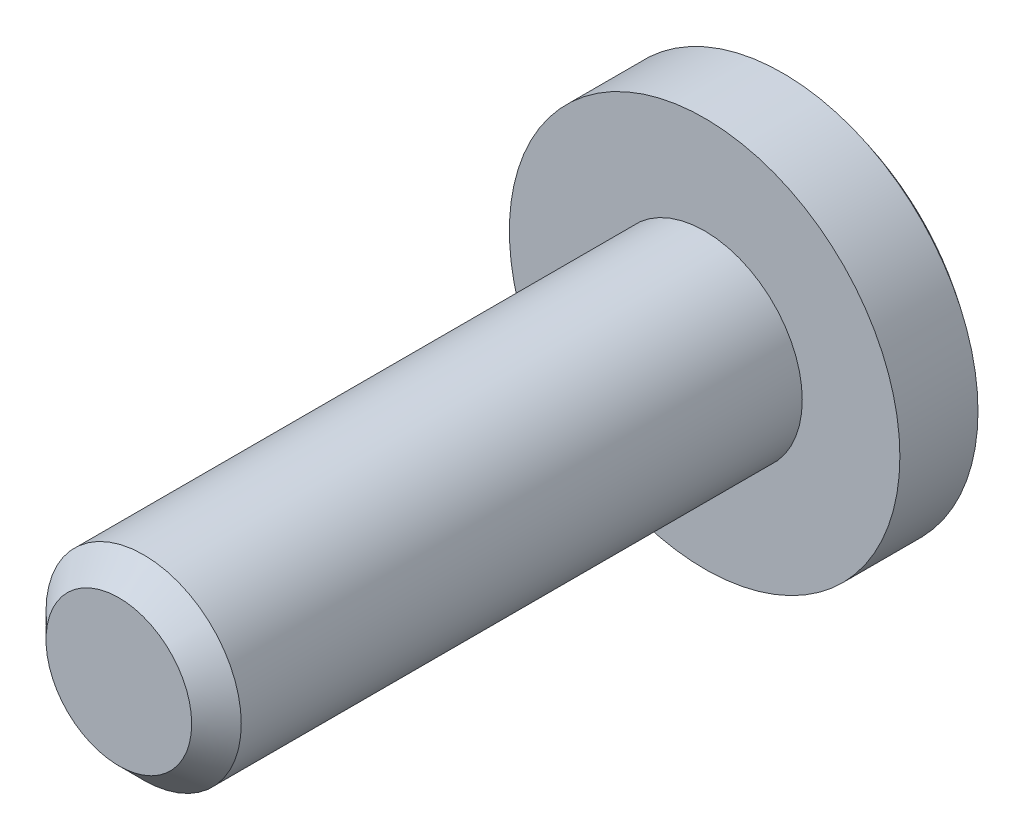
SolidWorks part; units mm, degrees
material "ASTM A36 Steel"
ref_plane "Front Plane" through (0, 0, 0) normal (0, 0, 1) x (1, 0, 0)
ref_plane "Top Plane" through (0, 0, 0) normal (0, 1, 0) x (1, 0, 0)
ref_plane "Right Plane" through (0, 0, 0) normal (1, 0, 0) x (0, 0, -1)
sketch "Sketch1" plane through (0, 0, 0) normal (0, 1, 0) x (1, 0, 0)
  line L0 (0, 0) -> (0, 7.5)
  line L1 (0, 0) -> (1, 0)
  line L2 (1, 0) -> (1, 6)
  line L3 (1, 6) -> (2, 6)
  line L4 (2, 6) -> (2, 6.8)
  line L5 (0, 7.5) -> (-1.075, 7.5) construction
  arc A0 (2, 6.8) -> (0, 7.5) centre (0, 4.2929) ccw
  dimension "D1" = 7.5
  dimension "D2" = 1
  dimension "D3" = 2
  dimension "D4" = 0.8
  dimension "D5" = 6
revolve "Revolve1" add sketch "Sketch1" angle 360 about L0
sketch "Sketch2" plane through (0, 0, 0) normal (0, 1, 0) x (1, 0, 0)
  line L0 (0, 6.8) -> (0, 0) construction
  line L1 (2, 6.8) -> (-2, 6.8) construction
  line L3 (0.3, 6.8) -> (-0.3, 6.8)
  line L4 (0.3, 6.8) -> (0.3, 8.3185)
  line L5 (0.3, 8.3185) -> (-0.3, 8.3185)
  line L6 (-0.3, 6.8) -> (-0.3, 8.3185)
  dimension "D1" = 0.6
extrude "Extrude1" cut sketch "Sketch2" against normal mid plane 2.54
sketch "Sketch3" plane through (0, 0, 0) normal (1, 0, 0) x (0, 0, -1)
  line L0 (0, 0) -> (6.8, 0) construction
  line L2 (6.8, 2) -> (6.8, -2) construction
  line L4 (6.8, 0.2945) -> (7.9032, 0.2945)
  line L5 (6.8, 0.2945) -> (6.8, -0.2945)
  line L6 (6.8, -0.2945) -> (7.9032, -0.2945)
  line L7 (7.9032, 0.2945) -> (7.9032, -0.2945)
extrude "Extrude2" cut sketch "Sketch3" against normal mid plane 2.54
chamfer "Chamfer1" distance 0.254 angle 45 1 edges at (1, 0, 0)
